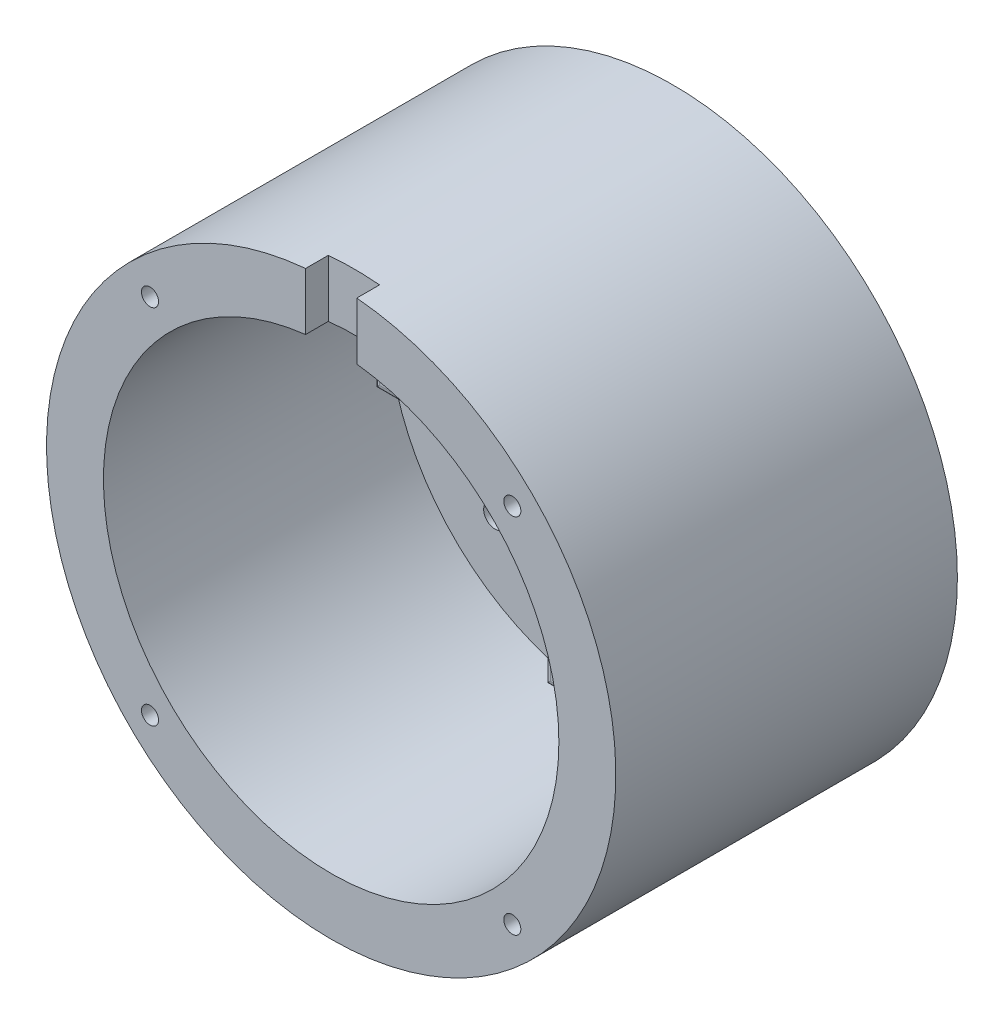
SolidWorks part; units mm, degrees
ref_plane "Alzado" through (0, 0, 0) normal (0, 0, 1) x (1, 0, 0)
ref_plane "Planta" through (0, 0, 0) normal (0, 1, 0) x (1, 0, 0)
ref_plane "Vista lateral" through (0, 0, 0) normal (1, 0, 0) x (0, 0, -1)
sketch "Croquis1" plane through (0, 0, 0) normal (0, 0, 1) x (1, 0, 0)
  circle A0 centre (0, 0) radius 50
  circle A1 centre (0, 0) radius 17.75
  dimension "D1" = 100
  dimension "D2" = 35.5
extrude "Saliente-Extruir1" add sketch "Croquis1" along normal blind 70
sketch "Croquis2" plane through (0, 0, 70) normal (0, 0, 1) x (1, 0, 0)
  circle A0 centre (0, 0) radius 40
  dimension "D1" = 80
extrude "Cortar-Extruir1" cut sketch "Croquis2" against normal blind 50
sketch "Croquis4" plane through (0, 0, 20) normal (0, 0, 1) x (1, 0, 0)
  line L1 (-2.5, 32.5) -> (2.5, 32.5)
  line L2 (-2.5, 32.5) -> (-2.5, 22.5)
  line L3 (-2.5, 22.5) -> (2.5, 22.5)
  line L4 (2.5, 32.5) -> (2.5, 22.5)
  line L5 (-2.5, 32.5) -> (2.5, 22.5) construction
  line L6 (-2.5, 22.5) -> (2.5, 32.5) construction
  line L7 (32.5, -2.5) -> (22.5, -2.5)
  line L8 (32.5, -2.5) -> (32.5, 2.5)
  line L9 (32.5, 2.5) -> (22.5, 2.5)
  line L10 (22.5, -2.5) -> (22.5, 2.5)
  line L11 (32.5, -2.5) -> (22.5, 2.5) construction
  line L12 (32.5, 2.5) -> (22.5, -2.5) construction
  line L13 (2.5, -32.5) -> (-2.5, -32.5)
  line L14 (2.5, -32.5) -> (2.5, -22.5)
  line L15 (2.5, -22.5) -> (-2.5, -22.5)
  line L16 (-2.5, -32.5) -> (-2.5, -22.5)
  line L17 (2.5, -32.5) -> (-2.5, -22.5) construction
  line L18 (2.5, -22.5) -> (-2.5, -32.5) construction
  line L19 (-32.5, -2.5) -> (-22.5, -2.5)
  line L20 (-32.5, -2.5) -> (-32.5, 2.5)
  line L21 (-32.5, 2.5) -> (-22.5, 2.5)
  line L22 (-22.5, -2.5) -> (-22.5, 2.5)
  line L23 (-32.5, -2.5) -> (-22.5, 2.5) construction
  line L24 (-32.5, 2.5) -> (-22.5, -2.5) construction
  circle A0 centre (0, 0) radius 40
  circle A1 centre (0, 0) radius 27.5
  point P4 (0, 27.5)
  point P9 (27.5, 0)
  point P14 (0, -27.5)
  point P19 (-27.5, 0)
  circle M10 centre (0, 0) radius 17.75
  circle M11 centre (0, 0) radius 40
  dimension "D1" = 80
  dimension "D2" = 55
  dimension "D3" = 10
  dimension "D4" = 5
  dimension "D5" = 5
  dimension "D6" = 10
  dimension "D7" = 5
  dimension "D8" = 10
  dimension "D9" = 5
  dimension "D10" = 10
extrude "Cortar-Extruir3" cut sketch "Croquis4" against normal blind 10 contours A1 L9 L8 L7 L14 L13 L16 L19 L20 L21 L2 L1 L4 M11 | L9 A1 L4 L3 L2 L21 L22 L19 L16 L15 L14 L7 L10 M10
sketch "Croquis5" plane through (0, 0, 10) normal (0, 0, 1) x (1, 0, 0)
  line L0 (0, 0) -> (28.2843, 28.2843) construction
  circle A0 centre (21.2132, 21.2132) radius 2
  circle A1 centre (21.2132, -21.2132) radius 2
  circle A2 centre (-21.2132, -21.2132) radius 2
  circle A3 centre (-21.2132, 21.2132) radius 2
  point P14 (0, 0)
  dimension "D2" = 4
  dimension "D1" = 40
  dimension "D4" = 30
  dimension "D3" = 4
extrude "Cortar-Extruir4" cut sketch "Croquis5" against normal through all
sketch "Croquis6" plane through (0, 0, 0) normal (0, 0, -1) x (-1, 0, 0)
  circle A0 centre (-21.2132, 21.2132) radius 5
  circle A1 centre (21.487, 21.487) radius 5
  circle A2 centre (21.7607, -21.2132) radius 5
  circle A3 centre (-20.9394, -21.487) radius 5
  point P12 (0.2738, 0)
  dimension "D1" = 10
  dimension "D2" = 4
extrude "Cortar-Extruir5" cut sketch "Croquis6" against normal blind 5
fillet "Redondeo2" radius 1 18 edges at (50, 0, 70) (40, 0, 70) (0, -22.5, 20) (2.5, -27.5, 20) (0, -32.5, 20) (-2.5, -27.5, 20) (-32.5, 0, 20) (-27.5, 2.5, 20) (-22.5, 0, 20) (-27.5, -2.5, 20) (22.5, 0, 20) (27.5, 2.5, 20) (32.5, 0, 20) (27.5, -2.5, 20) (0, 22.5, 20) (-2.5, 27.5, 20) (0, 32.5, 20) (2.5, 27.5, 20)
sketch "Croquis8" plane through (0, 0, 70) normal (0, 0, 1) x (1, 0, 0)
  line L0 (0, 0) -> (0, 52.9149) construction
  line L2 (-4.5, 55) -> (4.5, 55)
  line L3 (-4.5, 55) -> (-4.5, 35)
  line L4 (-4.5, 35) -> (4.5, 35)
  line L5 (4.5, 55) -> (4.5, 35)
  line L6 (-4.5, 55) -> (4.5, 35) construction
  line L7 (-4.5, 35) -> (4.5, 55) construction
  point P3 (0, 45)
  dimension "D1" = 9
  dimension "D2" = 20
  dimension "D3" = 45
extrude "Cortar-Extruir7" cut sketch "Croquis8" against normal blind 4 from offset 10 offset against normal yes
sketch "Croquis9" plane through (0, 0, 70) normal (0, 0, 1) x (1, 0, 0)
  circle A0 centre (0, 0) radius 52.3391
extrude "Cortar-Extruir8" cut sketch "Croquis9" against normal blind 10
sketch "Croquis10" plane through (0, 0, 60) normal (0, 0, 1) x (1, 0, 0)
  line L0 (0, 0) -> (50, 0) construction
  line L1 (0, 0) -> (35.3553, 35.3553) construction
  arc A0 (-4.5, 49.7971) -> (4.5, 49.7971) centre (0, 0) ccw construction
  circle A1 centre (31.8198, 31.8198) radius 1.5
  circle A2 centre (31.8198, -31.8198) radius 1.5
  circle A3 centre (-31.8198, -31.8198) radius 1.5
  circle A4 centre (-31.8198, 31.8198) radius 1.5
  point P19 (0, 0)
  dimension "D3" = 3
  dimension "D1" = 45
  dimension "D2" = 45
  dimension "D4" = 4
extrude "Cortar-Extruir9" cut sketch "Croquis10" against normal blind 30
